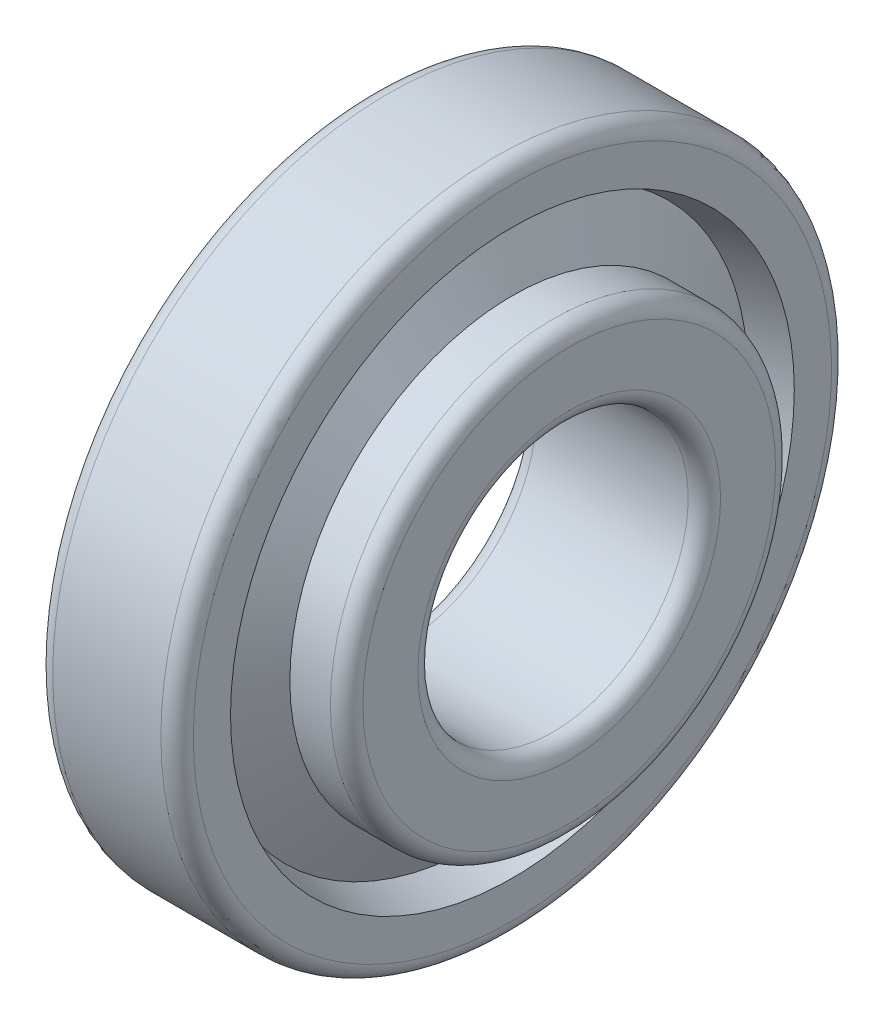
SolidWorks part; units mm, degrees
material "AISI Тип A2 Инструментальная сталь"
ref_plane "Спереди" through (0, 0, 0) normal (0, 0, 1) x (1, 0, 0)
ref_plane "Сверху" through (0, 0, 0) normal (0, 1, 0) x (1, 0, 0)
ref_plane "Справа" through (0, 0, 0) normal (1, 0, 0) x (0, 0, -1)
sketch "Эскиз1" plane through (0, 0, 0) normal (0, 0, 1) x (1, 0, 0)
  line L20 (-882.5277, 0) -> (43243.8573, 0) construction
  line L33 (5.4161, 23.7304) -> (0, 22.065)
  line L34 (0, 22.065) -> (0, 29.5)
  line L35 (1.5, 31) -> (11.5, 31)
  line L36 (13, 29.5) -> (13, 26.0624)
  line L37 (13, 26.0624) -> (9.7142, 25.0521)
  line L38 (5.4161, 23.7304) -> (9.7142, 25.0521) construction
  line L39 (9.5821, 16.1558) -> (1.25, 16.1558)
  line L40 (1.25, 16.1558) -> (1.25, 14)
  line L41 (2.75, 12.5) -> (16.75, 12.5)
  line L42 (18.25, 14) -> (18.25, 19.0779)
  line L43 (16.75, 20.5779) -> (13, 20.5779)
  line L44 (13, 20.5779) -> (13, 19.0779)
  line L45 (9.5821, 16.1558) -> (13, 19.0779) construction
  line L46 (13, 19.0779) -> (9.7142, 25.0521)
  line L47 (9.5821, 16.1558) -> (5.4161, 23.7304)
  line L48 (7.4991, 19.9431) -> (11.3571, 22.065) construction
  line L49 (0, 22.065) -> (11.3571, 22.065) construction
  line L50 (5.4161, 23.7304) -> (5.4161, 16.1558) construction
  arc A0 (0, 29.5) -> (1.5, 31) centre (1.5, 29.5) cw
  arc A1 (11.5, 31) -> (13, 29.5) centre (11.5, 29.5) cw
  arc A2 (1.25, 14) -> (2.75, 12.5) centre (2.75, 14) ccw
  arc A3 (18.25, 14) -> (16.75, 12.5) centre (16.75, 14) cw
  arc A4 (16.75, 20.5779) -> (18.25, 19.0779) centre (16.75, 19.0779) cw
  point P12 (11.3571, 22.065)
  dimension "гост r1" = 1.5
  dimension "гост r2" = 1.5
  dimension "гост DD" = 62
  dimension "гост B" = 17
  dimension "гост C" = 13
  dimension "гост T" = 18.25
  dimension "гост E" = 44.13
  dimension "гост d" = 25
  dimension "гост alfa" = 28.811
revolve "Повернуть1" add sketch "Эскиз1" angle 360 about L20
